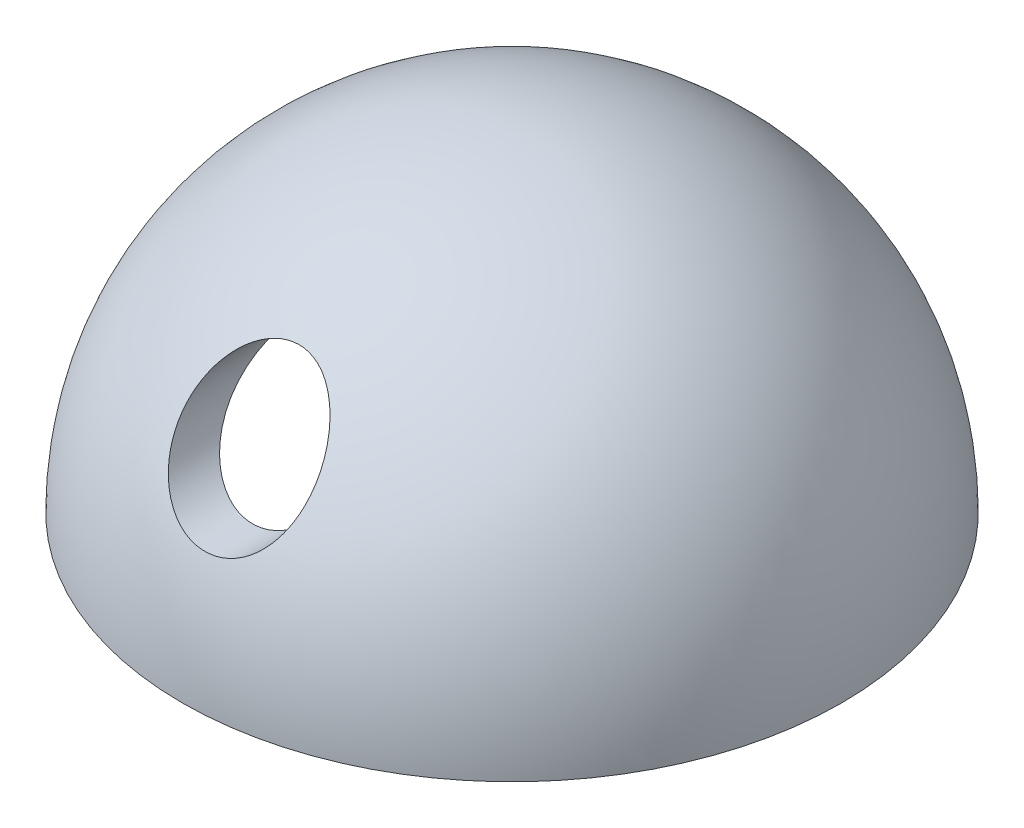
SolidWorks part; units mm, degrees
ref_plane "Alzado" through (0, 0, 0) normal (0, 0, 1) x (1, 0, 0)
ref_plane "Planta" through (0, 0, 0) normal (0, 1, 0) x (1, 0, 0)
ref_plane "Vista lateral" through (0, 0, 0) normal (1, 0, 0) x (0, 0, -1)
sketch "Croquis1" plane through (0, 0, 0) normal (0, 0, 1) x (1, 0, 0)
  line L0 (0, 0) -> (0, 15)
  line L1 (0, 0) -> (-15, 0)
  arc A0 (0, 15) -> (-15, 0) centre (0, 0) ccw
  dimension "D1" = 15
revolve "Revolución1" add sketch "Croquis1" angle 360 about L0
shell "Vaciado2" thickness 2
sketch "Croquis2" plane through (0, 0, 0) normal (0, 0, 1) x (1, 0, 0)
  circle A0 centre (0, 8.4565) radius 3
  dimension "D1" = 6
extrude "Cortar-Extruir1" cut sketch "Croquis2" along normal through all
